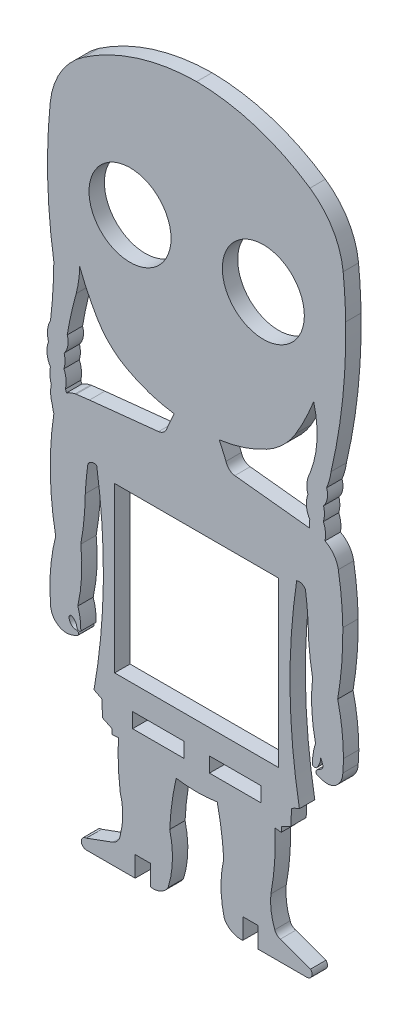
SolidWorks part; units mm, degrees
ref_plane "Alzado" through (0, 0, 0) normal (0, 0, 1) x (1, 0, 0)
ref_plane "Planta" through (0, 0, 0) normal (0, 1, 0) x (1, 0, 0)
ref_plane "Vista lateral" through (0, 0, 0) normal (1, 0, 0) x (0, 0, -1)
sketch "Model" plane through (0, 0, 0) normal (0, 0, 1) x (1, 0, 0)
  line L0 (62.5638, 42.4487) -> (63.8839, 39.4805)
  line L1 (65.5967, 37.9126) -> (80.1298, 36.3379)
  line L2 (34.4385, 36.1488) -> (34.6579, 36.1909)
  line L3 (34.6579, 36.1909) -> (37.2522, 36.5087)
  line L4 (37.2522, 36.5087) -> (50.7168, 37.9129)
  line L5 (52.4296, 39.4808) -> (53.7497, 42.4487)
  line L6 (70.6568, -11.9098) -> (60.6568, -11.9098)
  line L7 (60.6568, -11.9098) -> (60.6568, -14.8098)
  line L8 (60.6568, -14.8098) -> (70.6568, -14.8098)
  line L9 (70.6568, -14.8098) -> (70.6568, -11.9098)
  line L10 (45.6568, -14.8098) -> (55.6568, -14.8098)
  line L11 (55.6568, -14.8098) -> (55.6568, -11.9098)
  line L12 (55.6568, -11.9098) -> (45.6568, -11.9098)
  line L13 (45.6568, -11.9098) -> (45.6568, -14.8098)
  line L14 (74.1568, 24.8682) -> (74.1568, -7.1318)
  line L15 (74.1568, -7.1318) -> (42.1568, -7.1318)
  line L16 (42.1568, -7.1318) -> (42.1568, 24.8682)
  line L17 (42.1568, 24.8682) -> (74.1568, 24.8682)
  line L18 (38.1334, -11.989) -> (39.653, -12.7742)
  line L19 (39.653, -12.7742) -> (39.8029, -15.9123)
  line L20 (39.8029, -15.9123) -> (41.6594, -16.8123)
  line L21 (41.6594, -16.8123) -> (41.6596, -17.8123)
  line L22 (41.6596, -17.8123) -> (42.8851, -17.6861)
  line L23 (41.8217, -35.8969) -> (36.6196, -37.8057)
  line L24 (36.6628, -39.813) -> (46.1615, -39.8116)
  line L25 (46.1615, -39.8116) -> (46.1609, -35.8116)
  line L26 (46.1609, -35.8116) -> (49.1568, -35.8112)
  line L27 (49.1568, -35.8112) -> (49.1615, -39.8102)
  line L28 (67.1568, -39.8098) -> (67.1568, -35.8098)
  line L29 (67.1568, -35.8098) -> (70.1568, -35.8098)
  line L30 (70.1568, -35.8098) -> (70.1568, -39.8098)
  line L31 (70.1568, -39.8098) -> (79.6938, -39.8094)
  line L32 (80.377, -38.0546) -> (74.4777, -35.9339)
  line L33 (73.4299, -17.6839) -> (74.6555, -17.8098)
  line L34 (74.6555, -17.8098) -> (74.6555, -16.8098)
  line L35 (74.6555, -16.8098) -> (76.5119, -15.9096)
  line L36 (76.5119, -15.9096) -> (76.6613, -12.7715)
  line L37 (82.3659, -1.3556) -> (82.7315, -2.3376)
  circle A0 centre (45.1568, 71.7122) radius 8
  circle A1 centre (71.1568, 71.7122) radius 8
  arc A2 (80.2563, 45.6766) -> (79.8511, 41.8401) centre (84.8425, 43.2525) ccw
  arc A3 (80.2563, 45.6766) -> (80.9785, 58.1128) centre (61.9028, 52.9814) ccw
  arc A4 (77.4999, 50.9639) -> (80.9785, 58.1128) centre (36.4749, 75.3469) ccw
  arc A5 (71.8183, 45.4757) -> (77.4999, 50.9639) centre (64.6054, 58.6276) ccw
  arc A6 (62.5638, 42.4487) -> (71.8183, 45.4757) centre (59.1269, 68.617) ccw
  arc A7 (63.8839, 39.4805) -> (65.5967, 37.9126) centre (65.8399, 39.8977) ccw
  arc A8 (80.2197, 37.7903) -> (80.1298, 36.3379) centre (86.2192, 36.6902) ccw
  arc A9 (79.8511, 41.8401) -> (80.2197, 37.7903) centre (84.1555, 40.1902) ccw
  arc A10 (34.6555, 53.1902) -> (35.3465, 58.0834) centre (13.6317, 58.6543) ccw
  arc A11 (34.6555, 53.1902) -> (32.9044, 45.3348) centre (108.4318, 32.6211) ccw
  arc A12 (32.3073, 41.985) -> (32.9044, 45.3348) centre (29.5546, 44.2037) ccw
  arc A13 (32.2737, 39.3029) -> (32.3073, 41.985) centre (27.5137, 40.7037) ccw
  arc A14 (32.5504, 36.0037) -> (32.2737, 39.3029) centre (27.3791, 37.2312) ccw
  arc A15 (32.7631, 35.4684) -> (32.5504, 36.0037) centre (27.5274, 33.6971) ccw
  arc A16 (34.4385, 36.1488) -> (32.7631, 35.4684) centre (35.4512, 31.2524) ccw
  arc A17 (50.7168, 37.9129) -> (52.4296, 39.4808) centre (50.4736, 39.898) ccw
  arc A18 (44.4952, 45.4757) -> (53.7497, 42.4487) centre (57.1866, 68.617) ccw
  arc A19 (38.8136, 50.9639) -> (44.4952, 45.4757) centre (51.7081, 58.6276) ccw
  arc A20 (35.3465, 58.0834) -> (38.8136, 50.9639) centre (79.8386, 75.3469) ccw
  arc A21 (29.6555, 46.1902) -> (30.295, 56.3931) centre (-64.2835, 57.1992) ccw
  arc A22 (29.6555, 46.1902) -> (29.2503, 42.3536) centre (34.2417, 43.7661) ccw
  arc A23 (29.2503, 42.3536) -> (29.6188, 38.3039) centre (33.5546, 40.7037) ccw
  arc A24 (29.6188, 38.3039) -> (29.8024, 35.3655) centre (35.6183, 37.2037) ccw
  arc A25 (29.8024, 35.3655) -> (30.0008, 32.101) centre (35.6688, 34.0838) ccw
  arc A26 (30.0008, 32.101) -> (30.2991, 30.7378) centre (36.0082, 32.7014) ccw
  arc A27 (30.2991, 30.7378) -> (30.6555, 10.1902) centre (90.5859, 21.5066) ccw
  arc A28 (30.6555, 10.1902) -> (29.6555, -1.8098) centre (66.1555, 1.1902) ccw
  arc A29 (29.6555, -1.8098) -> (30.5009, -4.0446) centre (33.0947, -1.786) ccw
  arc A30 (30.5009, -4.0446) -> (33.3917, -5.008) centre (32.7634, -2.0745) ccw
  arc A31 (33.3917, -5.008) -> (34.843, -4.4671) centre (32.275, 0.2057) ccw
  arc A32 (34.843, -4.4671) -> (34.7392, -3.6139) centre (34.6883, -4.053) ccw
  arc A33 (33.2831, -2.1093) -> (34.7392, -3.6139) centre (34.6914, -2.2033) ccw
  arc A34 (33.9383, -1.7453) -> (33.2831, -2.1093) centre (33.6957, -2.0802) ccw
  arc A35 (34.7877, -3.0557) -> (33.9383, -1.7453) centre (32.7792, -3.4271) ccw
  arc A36 (34.7877, -3.0557) -> (35.3874, -3.4976) centre (35.2766, -3.0201) ccw
  arc A37 (35.3874, -3.4976) -> (35.5552, -3.3803) centre (35.117, -2.9322) ccw
  arc A38 (35.5552, -3.3803) -> (34.9755, 0.5706) centre (24.1442, -3.0366) ccw
  arc A39 (34.9755, 0.5706) -> (35.5559, 11.3015) centre (2.8291, 7.6905) ccw
  arc A40 (35.5559, 11.3015) -> (36.4293, 20.2669) centre (-16.3594, 20.8843) ccw
  arc A41 (36.9426, 25.5844) -> (36.4293, 20.2669) centre (99.7291, 16.84) ccw
  arc A42 (38.6555, 26.1902) -> (36.9426, 25.5844) centre (38.1555, 24.8795) ccw
  arc A43 (38.1334, -11.989) -> (38.6555, 26.1902) centre (-77.8445, 8.6902) ccw
  arc A44 (42.8851, -17.6861) -> (43.2401, -26.7421) centre (96.98, -20.1005) ccw
  arc A45 (43.2771, -33.832) -> (43.2401, -26.7421) centre (30.4973, -30.3536) ccw
  arc A46 (41.8217, -35.8969) -> (43.2771, -33.832) centre (40.8857, -33.6919) ccw
  arc A47 (36.6196, -37.8057) -> (36.6628, -39.813) centre (36.6527, -38.8091) ccw
  arc A48 (49.1615, -39.8102) -> (52.5765, -38.2242) centre (49.6223, -36.3329) ccw
  arc A49 (52.5765, -38.2242) -> (52.8963, -28.1997) centre (34.916, -32.6434) ccw
  arc A50 (54.1539, -18.9192) -> (52.8963, -28.1997) centre (106.3042, -30.7116) ccw
  arc A51 (54.1539, -18.9192) -> (62.1613, -18.9186) centre (58.1558, 6.2115) ccw
  arc A52 (63.4347, -27.9515) -> (62.1613, -18.9186) centre (5.2363, -31.5495) ccw
  arc A53 (63.4347, -27.9515) -> (63.5458, -37.9109) centre (84.3288, -32.6988) ccw
  arc A54 (63.5458, -37.9109) -> (67.1568, -39.8098) centre (66.7308, -36.2371) ccw
  arc A55 (79.6938, -39.8094) -> (80.377, -38.0546) centre (79.625, -38.7723) ccw
  arc A56 (73.3908, -34.8931) -> (74.4777, -35.9339) centre (74.8588, -34.4479) ccw
  arc A57 (72.6274, -29.23) -> (73.3908, -34.8931) centre (85.0257, -30.4418) ccw
  arc A58 (72.6274, -29.23) -> (73.4299, -17.6839) centre (23.4166, -20.0085) ccw
  arc A59 (78.199, -12.0467) -> (76.6613, -12.7715) centre (80.3297, -18.5601) ccw
  arc A60 (77.658, 26.1902) -> (78.199, -12.0467) centre (194.343, 8.7188) ccw
  arc A61 (79.3709, 25.5844) -> (77.658, 26.1902) centre (78.158, 24.8795) ccw
  arc A62 (79.8842, 20.2669) -> (79.3709, 25.5844) centre (16.5844, 16.84) ccw
  arc A63 (79.8842, 20.2669) -> (80.7566, 11.3008) centre (132.6769, 20.8783) ccw
  arc A64 (80.7566, 11.3008) -> (81.3367, 0.5698) centre (113.6888, 7.6997) ccw
  arc A65 (81.3367, 0.5698) -> (80.7512, -3.3755) centre (92.4245, -3.0916) ccw
  arc A66 (80.7512, -3.3755) -> (81.5434, -3.4575) centre (81.1978, -2.929) ccw
  arc A67 (81.5434, -3.4575) -> (82.3659, -1.3556) centre (78.7702, -1.1605) ccw
  arc A68 (82.3482, -3.3063) -> (82.7315, -2.3376) centre (81.9631, -2.5937) ccw
  arc A69 (82.3482, -3.3063) -> (81.5193, -3.8695) centre (84.7025, -7.6629) ccw
  arc A70 (81.5193, -3.8695) -> (81.5949, -4.5977) centre (81.883, -4.1998) ccw
  arc A71 (81.5949, -4.5977) -> (83.5463, -5.1232) centre (83.9702, 0.3367) ccw
  arc A72 (83.5463, -5.1232) -> (85.8126, -4.0446) centre (83.5724, -2.258) ccw
  arc A73 (85.8126, -4.0446) -> (86.658, -1.8098) centre (83.2188, -1.786) ccw
  arc A74 (86.658, -1.8098) -> (86.7777, 0.6902) centre (50.158, 1.1902) ccw
  arc A75 (86.7777, 0.6902) -> (85.658, 10.1902) centre (45.9158, 0.6902) ccw
  arc A76 (85.658, 10.1902) -> (86.66, 22.7527) centre (17.3322, 21.961) ccw
  arc A77 (86.66, 22.7527) -> (85.786, 32.1228) centre (22.8163, 21.5236) ccw
  arc A78 (85.786, 32.1228) -> (83.192, 35.6766) centre (80.8623, 31.2524) ccw
  arc A79 (83.192, 35.6766) -> (82.8746, 38.7893) centre (77.9799, 36.7177) ccw
  arc A80 (82.8746, 38.7893) -> (82.9081, 41.4714) centre (78.1145, 40.1902) ccw
  arc A81 (82.9081, 41.4714) -> (83.5052, 44.8212) centre (80.1555, 43.6902) ccw
  arc A82 (83.5052, 44.8212) -> (84.3644, 47.9622) centre (72.4924, 49.5217) ccw
  arc A83 (84.3644, 47.9622) -> (87.2248, 74.6898) centre (-22.1643, 72.8798) ccw
  arc A84 (87.2248, 74.6898) -> (86.7283, 82.906) centre (-18.1174, 72.4467) ccw
  arc A85 (86.7283, 82.906) -> (80.2556, 93.8082) centre (71.8024, 81.417) ccw
  arc A86 (80.2556, 93.8082) -> (58.1568, 100.7515) centre (57.7506, 60.8192) ccw
  arc A87 (58.1568, 100.7515) -> (36.0579, 93.8082) centre (58.5629, 60.8192) ccw
  arc A88 (36.0579, 93.8082) -> (29.5852, 82.906) centre (44.5111, 81.417) ccw
  arc A89 (29.5852, 82.906) -> (30.295, 56.3931) centre (134.4309, 72.4467) ccw
extrude "Saliente-Extruir1" add sketch "Model" along normal blind 3
